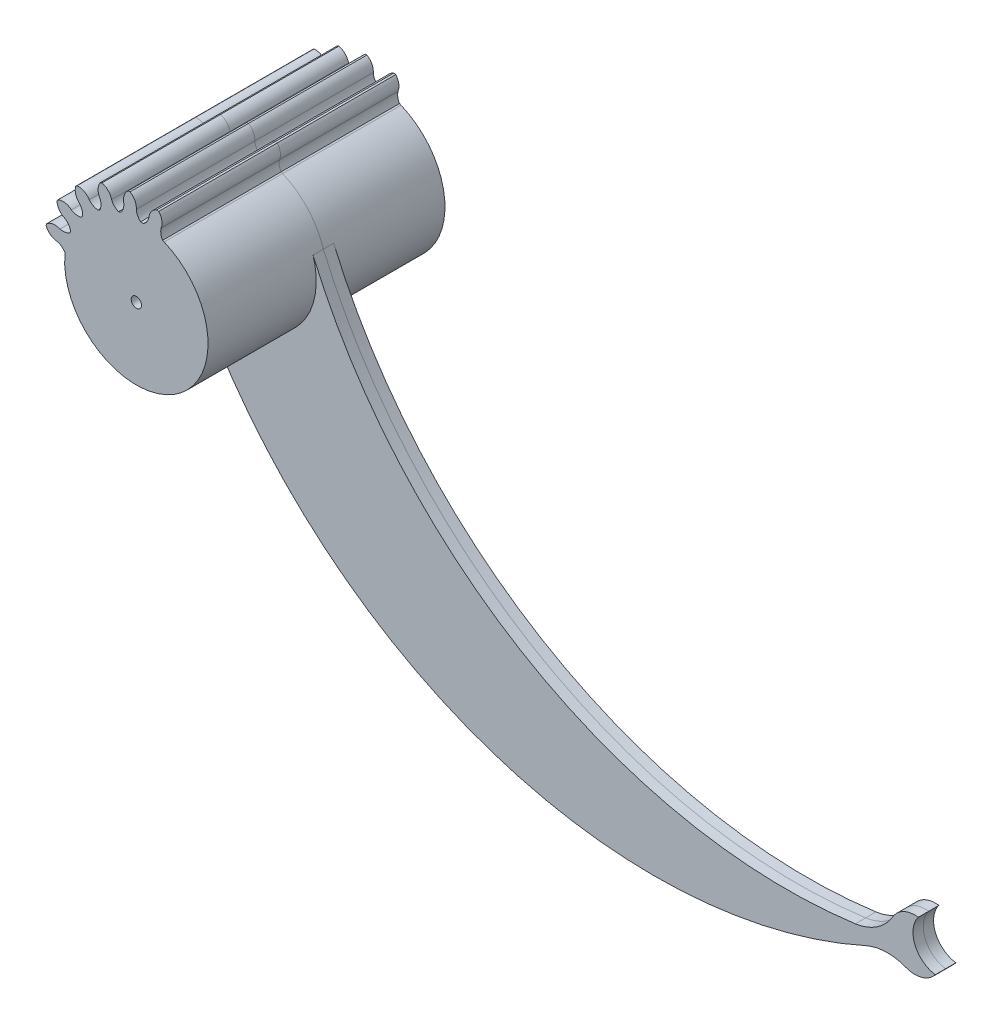
SolidWorks part; units mm, degrees
ref_plane "Plan de face" through (0, 0, 0) normal (0, 0, 1) x (1, 0, 0)
ref_plane "Plan de dessus" through (0, 0, 0) normal (0, 1, 0) x (1, 0, 0)
ref_plane "Plan de droite" through (0, 0, 0) normal (1, 0, 0) x (0, 0, -1)
sketch "Esquisse1" plane through (0, 0, 0) normal (0, 0, 1) x (1, 0, 0)
  circle A0 centre (0, 0) radius 18
extrude "Boss.-Extru.1" add sketch "Esquisse1" against normal blind 23
sketch "Esquisse3" plane through (0, 0, -23) normal (0, 0, -1) x (-1, 0, 0)
  line L0 (-5.4964, 12.79) -> (-5.1005, 12.9694)
  line L1 (-1.4153, 13.9392) -> (-0.828, 13.9392)
  line L2 (3.4609, 13.4999) -> (2.9859, 13.6442)
  line L3 (7.0639, 12.0036) -> (7.4657, 11.7813)
  line L4 (10.417, 9.2257) -> (10.7311, 8.9116)
  line L5 (12.9063, 5.2048) -> (12.7653, 5.634)
  line L6 (13.8895, 0.9713) -> (13.8895, 1.4478)
  arc A0 (-7.2352, 14.2707) -> (15.9996, 0.1072) centre (0, 0) ccw
  arc A2 (3.4609, 13.4999) -> (4.9239, 15.2235) centre (2.4924, 15.8047) ccw
  arc A3 (7.0585, 13.9223) -> (7.2352, 14.2707) centre (4.9239, 15.2235) ccw
  arc A4 (7.4657, 11.7813) -> (9.3698, 12.9694) centre (7.2352, 14.2707) ccw
  arc A5 (11.0004, 11.0744) -> (9.4294, 15.4687) centre (9.3698, 12.9694) ccw
  arc A6 (10.7311, 8.9116) -> (12.9063, 9.4565) centre (11.2757, 11.3516) ccw
  arc A7 (13.8747, 7.1517) -> (13.7322, 11.8162) centre (12.9063, 9.4565) ccw
  arc A8 (12.9063, 5.2048) -> (15.1902, 5.0258) centre (14.2219, 7.3307) ccw
  arc A9 (-0.828, 13.9392) -> (0, 16) centre (-2.4924, 15.8047) ccw
  arc A10 (-2.4315, 15.4188) -> (-6.9047, 16.7487) centre (-4.9239, 15.2235) ccw
  arc A11 (-5.1005, 12.9694) -> (-4.9239, 15.2235) centre (-7.2352, 14.2707) ccw
  arc A12 (-7.0585, 13.9223) -> (-9.4294, 15.4687) centre (-9.3698, 12.9694) ccw
  arc A13 (15.4022, 2.5348) -> (16.7021, 7.0168) centre (15.1902, 5.0258) ccw
  arc A14 (13.8895, 0.9713) -> (15.9996, 0.1072) centre (15.7876, 2.5982) ccw
  arc A15 (15.7876, 2.5982) -> (13.8895, 1.4478) centre (15.9996, 0.1072) ccw
  arc A16 (18.0699, -1.2942) -> (15.609, 0.1046) centre (15.821, -2.3864) ccw
  arc A17 (-7.2352, 14.2707) -> (-5.4964, 12.79) centre (-4.9239, 15.2235) ccw
  arc A18 (-6.9047, 16.7487) -> (-9.4294, 15.4687) centre (-7.2352, 14.2707) ccw
  arc A19 (-2.4924, 15.8047) -> (-1.4153, 13.9392) centre (0, 16) ccw
  arc A20 (-1.4153, 18.0608) -> (-4.8037, 14.8519) centre (-2.4924, 15.8047) ccw
  arc A21 (-2.4924, 15.8047) -> (-4.9239, 15.2235) centre (0, 0) ccw
  arc A22 (1.4153, 18.0608) -> (-1.4153, 18.0608) centre (0, 16) ccw
  arc A24 (7.0585, 13.9223) -> (4.2114, 17.6199) centre (4.9239, 15.2235) ccw
  arc A25 (3.4609, 13.4999) -> (4.9239, 15.2235) centre (2.4924, 15.8047) ccw
  arc A26 (-2.4924, 15.8047) -> (-1.4153, 13.9392) centre (0, 16) ccw
  arc A27 (2.4315, 15.4188) -> (-1.4153, 18.0608) centre (0, 16) ccw
  arc A28 (2.4924, 15.8047) -> (2.9859, 13.6442) centre (4.9239, 15.2235) ccw
  arc A29 (4.2114, 17.6199) -> (0, 15.6094) centre (2.4924, 15.8047) ccw
  arc A30 (4.2114, 17.6199) -> (0, 15.6094) centre (2.4924, 15.8047) ccw
  arc A31 (2.4924, 15.8047) -> (0, 16) centre (0, 0) ccw
  arc A32 (7.2352, 14.2707) -> (7.0639, 12.0036) centre (9.3698, 12.9694) ccw
  arc A33 (9.4294, 15.4687) -> (4.8037, 14.8519) centre (7.2352, 14.2707) ccw
  arc A34 (11.2757, 11.3516) -> (10.417, 9.2257) centre (12.9063, 9.4565) ccw
  arc A35 (13.7322, 11.8162) -> (9.1411, 12.6528) centre (11.2757, 11.3516) ccw
  arc A36 (7.2352, 14.2707) -> (4.9239, 15.2235) centre (0, 0) ccw
  arc A37 (11.2757, 11.3516) -> (9.3698, 12.9694) centre (0, 0) ccw
  arc A38 (14.2219, 7.3307) -> (12.7653, 5.634) centre (15.1902, 5.0258) ccw
  arc A39 (14.2219, 7.3307) -> (12.9063, 9.4565) centre (0, 0) ccw
  arc A40 (16.7021, 7.0168) -> (12.5913, 9.2257) centre (14.2219, 7.3307) ccw
  arc A41 (18.0509, 1.5363) -> (14.8193, 4.9031) centre (15.7876, 2.5982) ccw
  arc A42 (15.7876, 2.5982) -> (15.1902, 5.0258) centre (0, 0) ccw
  arc A43 (18.0699, -1.2942) -> (18.0509, 1.5363) centre (15.9996, 0.1072) ccw
  circle A44 centre (0, 0) radius 1
  circle A45 centre (0, 0) radius 13.9234
  circle M5 centre (0, 0) radius 18
extrude "Enlèv. mat.-Extru.3" cut sketch "Esquisse3" against normal through all contours A20 A12 A17 L0 A11 M5 | A20 A10 A18 A12 M5 | A29 A10 A19 L1 A9 M5 | A29 A22 A20 A10 M5 | A33 A27 A28 L2 A2 M5 | A33 A24 A29 A27 M5 | A35 A24 A3 A32 L3 A4 M5 | A35 A5 A33 A24 M5 | A40 A5 A34 L4 A6 M5 | A40 A7 A35 A5 M5 | A41 A7 A38 L5 A8 M5 | A41 A13 A40 A7 M5 | A16 A13 A15 L6 A14 M5 | A16 A43 A41 A13 M5 | A44 | A16 A0 A12 M5 | A45 A17 A0 A14 | A12 A17 | A14 A16
sketch "Esquisse4" plane through (0, 0, -23) normal (0, 0, -1) x (-1, 0, 0)
  line L0 (6.8604, 16.6414) -> (0, 0) construction
  line L1 (-130.1688, -53.4545) -> (-92.4244, 38.1021) construction
  line L2 (0, 0) -> (-5.3067, -12.8724) construction
  line L3 (12.8724, -5.3067) -> (0, 0) construction
  line L4 (0, 0) -> (-12.8724, 5.3067) construction
  line L5 (-12.8724, 5.3067) -> (-597.4932, 246.3176) construction
  line L6 (-130.1688, -53.4545) -> (-191.9541, -27.9834) construction
  arc A0 (7.03, 16.5704) -> (6.6901, 16.7105) centre (0, 0) ccw construction
  arc A3 (-5.4019, 12.8328) -> (13.8895, 0.9713) centre (0, 0) ccw construction
  circle A4 centre (-105.26, 43.3936) radius 100
  circle A5 centre (-79.5888, 32.8106) radius 100
  circle A6 centre (-130.1688, -53.4545) radius 5
  circle A7 centre (-134.7914, -51.5488) radius 5
  point P4 (-130.1688, -53.4545)
  arc M8 (-5.4019, 12.8328) -> (13.8895, 0.9713) centre (0, 0) ccw
  dimension "D2" = 90
  dimension "D1" = 90
extrude "Boss.-Extru.2" add sketch "Esquisse4" against normal blind 2 separate body contours A6 A5 A4 M8 | A7 A6 A5 | A7 A4 A6 | A5 A6 A4
mirror "Symétrie1" about plane through (0, 0, -23) normal (0, 0, 1) of bodies 104 108
fillet "Congé1" radius 10 2 edges at (125.2968, -54.5785, -22) (125.7936, -55.8748, -22)
fillet "Congé2" radius 10 2 edges at (125.2968, -54.5785, -24) (125.7936, -55.8748, -24)
